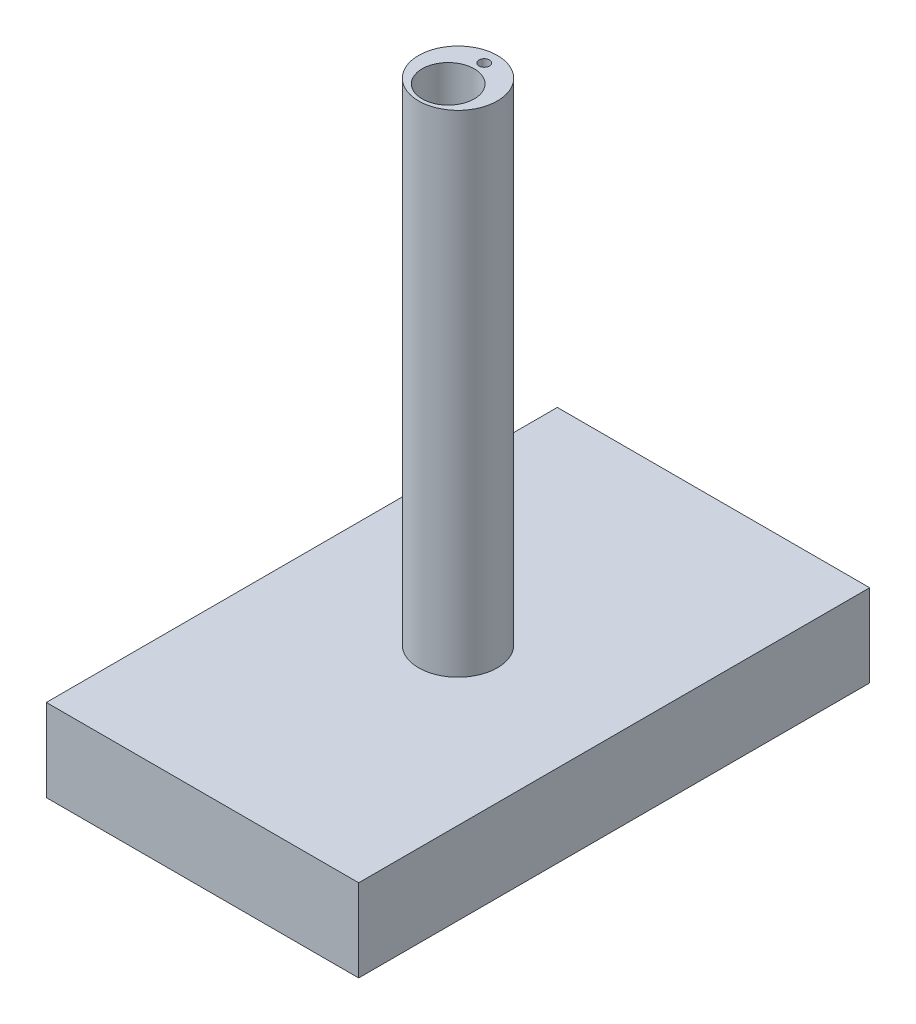
SolidWorks part; units mm, degrees
ref_plane "Front Plane" through (0, 0, 0) normal (0, 0, 1) x (1, 0, 0)
ref_plane "Top Plane" through (0, 0, 0) normal (0, 1, 0) x (1, 0, 0)
ref_plane "Right Plane" through (0, 0, 0) normal (1, 0, 0) x (0, 0, -1)
sketch "Sketch1" plane through (0, 0, 0) normal (0, 1, 0) x (1, 0, 0)
  circle A0 centre (0, 0) radius 28.1
extrude "Boss-Extrude1" add sketch "Sketch1" along normal blind 350
sketch "Sketch2" plane through (0, 350, 0) normal (0, 1, 0) x (1, 0, 0)
  circle A0 centre (0, -7) radius 18.6
extrude "Cut-Extrude1" cut sketch "Sketch2" against normal blind 58.8
sketch "Sketch3" plane through (0, 0, 0) normal (0, -1, 0) x (-1, 0, 0)
  line L1 (111.3415, -182.1414) -> (-111.3415, -182.1414)
  line L2 (111.3415, -182.1414) -> (111.3415, 182.1414)
  line L3 (111.3415, 182.1414) -> (-111.3415, 182.1414)
  line L4 (-111.3415, -182.1414) -> (-111.3415, 182.1414)
  line L5 (111.3415, -182.1414) -> (-111.3415, 182.1414) construction
  line L6 (111.3415, 182.1414) -> (-111.3415, -182.1414) construction
  point P0 (0, 0)
extrude "Boss-Extrude2" add sketch "Sketch3" along normal blind 58.8
sketch "Sketch4" plane through (0, -58.8, 0) normal (0, -1, 0) x (-1, 0, 0)
  line L1 (103.9587, -174.2721) -> (-103.9587, -174.2721)
  line L2 (103.9587, -174.2721) -> (103.9587, 174.2721)
  line L3 (103.9587, 174.2721) -> (-103.9587, 174.2721)
  line L4 (-103.9587, -174.2721) -> (-103.9587, 174.2721)
  line L5 (103.9587, -174.2721) -> (-103.9587, 174.2721) construction
  line L6 (103.9587, 174.2721) -> (-103.9587, -174.2721) construction
  point P0 (0, 0)
extrude "Cut-Extrude2" cut sketch "Sketch4" against normal blind 48.8
sketch "Sketch5" plane through (0, 291.2, 0) normal (0, 1, 0) x (1, 0, 0)
  circle A1 centre (0, -7) radius 16.1
extrude "Cut-Extrude3" cut sketch "Sketch5" against normal blind 350
sketch "Sketch6" plane through (0, 350, 0) normal (0, 1, 0) x (1, 0, 0)
  circle A1 centre (0, 18.75) radius 3.75
extrude "Cut-Extrude5" cut sketch "Sketch6" against normal blind 400
